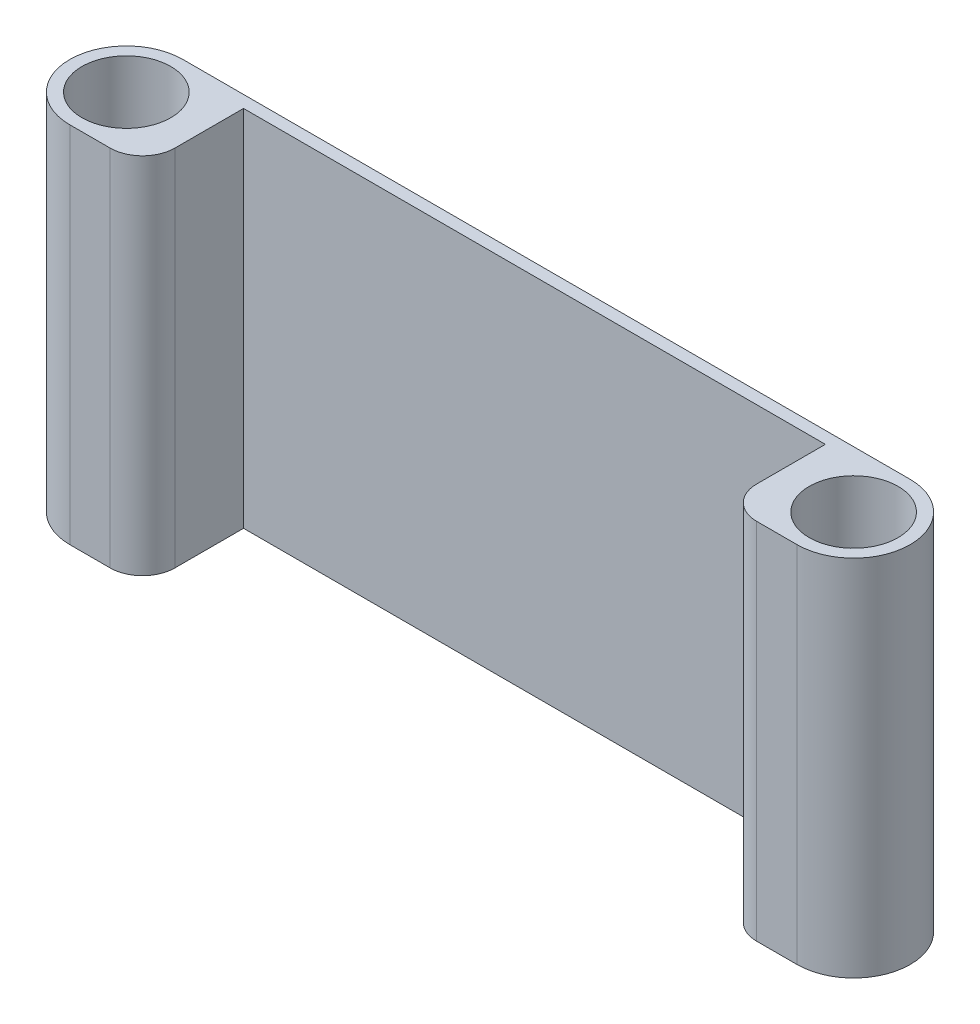
SolidWorks part; units mm, degrees
ref_plane "Front Plane" through (0, 0, 0) normal (0, 0, 1) x (1, 0, 0)
ref_plane "Top Plane" through (0, 0, 0) normal (0, 1, 0) x (1, 0, 0)
ref_plane "Right Plane" through (0, 0, 0) normal (1, 0, 0) x (0, 0, -1)
sketch "Sketch1" plane through (0, 0, 0) normal (0, 1, 0) x (1, 0, 0)
  line L0 (137.4606, -14.5) -> (119.4606, -14.5)
  line L1 (119.4606, -14.5) -> (119.4606, 10.5)
  line L2 (-42.5394, -14.5) -> (-24.5394, -14.5)
  line L3 (-42.5394, 13.5) -> (137.4606, 13.5)
  line L4 (119.4606, 10.5) -> (-24.5394, 10.5)
  line L5 (-24.5394, -14.5) -> (-24.5394, 10.5)
  circle A0 centre (-42.5394, -0.5) radius 11
  circle A1 centre (137.4606, -0.5) radius 11
  arc A2 (-42.5394, -14.5) -> (-42.5394, 13.5) centre (-42.5394, -0.5) cw
  arc A6 (137.4606, 13.5) -> (137.4606, -14.5) centre (137.4606, -0.5) cw
  dimension "D3" = 22
  dimension "D4" = 22
  dimension "D5" = 180
  dimension "D6" = 3
  dimension "D1" = 18
  dimension "D2" = 18
  dimension "D8" = 3
extrude "Boss-Extrude1" add sketch "Sketch1" along normal blind 90
fillet "Fillet1" radius 8 2 edges at (119.4606, 45, 14.5) (-24.5394, 45, 14.5)
